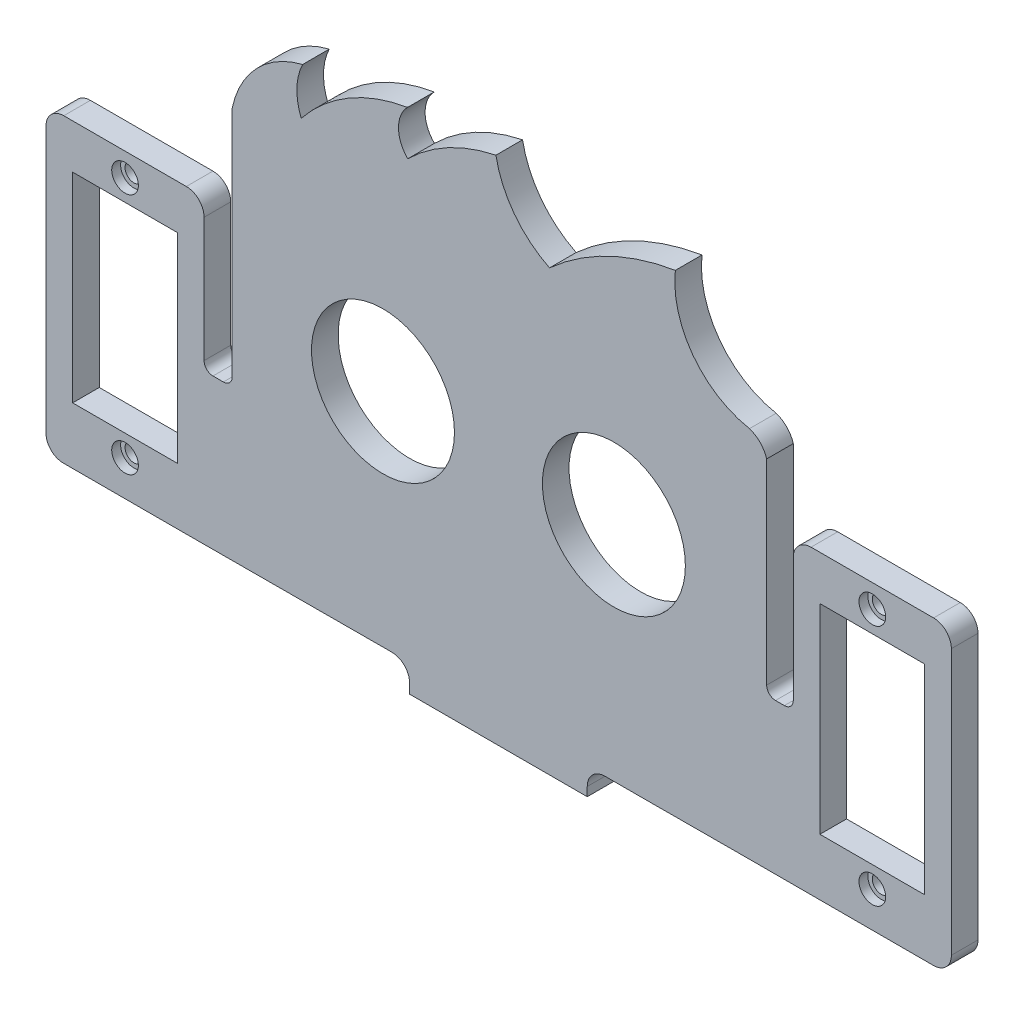
SolidWorks part; units mm, degrees
ref_plane "Alzado" through (0, 0, 0) normal (0, 0, 1) x (1, 0, 0)
ref_plane "Planta" through (0, 0, 0) normal (0, 1, 0) x (1, 0, 0)
ref_plane "Vista lateral" through (0, 0, 0) normal (1, 0, 0) x (0, 0, -1)
sketch "Model" plane through (0, 0, 0) normal (0, 0, 1) x (1, 0, 0)
  line L0 (28.5553, -36.0989) -> (29.723, -36.0989)
  line L4 (27.5553, -21.121) -> (27.5553, -35.0989)
  line L7 (70.699, -56.058) -> (50.699, -56.058)
  line L8 (92.899, -36.071) -> (91.899, -36.071)
  line L11 (90.899, -13.021) -> (90.899, -35.071)
  line L14 (96.899, -46.621) -> (108.699, -46.621)
  line L15 (108.699, -46.621) -> (108.699, -24.121)
  line L16 (108.699, -24.121) -> (96.899, -24.121)
  line L17 (96.899, -24.121) -> (96.899, -46.621)
  line L18 (12.7553, -24.121) -> (12.7553, -46.621)
  line L19 (12.7553, -46.621) -> (24.5553, -46.621)
  line L20 (24.5553, -46.621) -> (24.5553, -24.121)
  line L21 (24.5553, -24.121) -> (12.7553, -24.121)
  line L22 (93.899, -35.071) -> (93.899, -21.121)
  line L26 (72.699, -53.058) -> (76.899, -53.058)
  line L27 (73.699, -28.021) -> (47.699, -28.021) construction
  line L28 (60.699, -28.021) -> (60.699, -66.5104) construction
  line L29 (60.699, -56.058) -> (60.699, -18.5514) construction
  line L30 (70.699, -56.058) -> (70.699, -55.058)
  line L31 (50.699, -56.058) -> (50.699, -54.9616)
  line L32 (25.6116, -53.0206) -> (48.6939, -52.9617)
  line L53 (30.723, -8.8986) -> (30.723, -35.0989)
  line L55 (88.899, -53.021) -> (76.899, -53.058)
  line L61 (109.699, -19.121) -> (95.899, -19.121)
  line L62 (111.699, -51.021) -> (111.699, -21.121)
  line L63 (109.699, -53.021) -> (88.899, -53.021)
  line L95 (9.7553, -21.121) -> (9.7553, -51.0769)
  line L96 (25.5553, -19.121) -> (11.7553, -19.121)
  line L98 (25.6116, -53.0206) -> (11.699, -53.0206)
  circle A8 centre (73.699, -28.021) radius 8.05
  circle A9 centre (47.699, -28.021) radius 8.05
  circle A10 centre (102.799, -21.721) radius 1
  circle A11 centre (102.799, -49.021) radius 1
  circle A12 centre (18.6553, -49.021) radius 1
  circle A13 centre (18.6553, -21.721) radius 1
  arc A14 (91.899, -36.071) -> (90.899, -35.071) centre (91.899, -35.071) cw
  arc A15 (92.899, -36.071) -> (93.899, -35.071) centre (92.899, -35.071) ccw
  arc A16 (29.723, -36.0989) -> (30.723, -35.0989) centre (29.723, -35.0989) ccw
  arc A17 (28.5553, -36.0989) -> (27.5553, -35.0989) centre (28.5553, -35.0989) cw
  arc A18 (50.699, -54.9616) -> (48.6939, -52.9617) centre (48.699, -54.9616) ccw
  arc A19 (70.699, -55.058) -> (72.699, -53.058) centre (72.699, -55.058) cw
  arc A35 (38.6464, -0.6811) -> (30.723, -8.8986) centre (41.1528, -11.0265) ccw
  arc A36 (38.6464, -0.6811) -> (38.4994, -6.0039) centre (44.5214, -3.5068) ccw
  arc A37 (50.467, 1.0514) -> (38.4994, -6.0039) centre (53.655, -18.0341) ccw
  arc A38 (50.467, 1.0514) -> (50.49, -3.9486) centre (52.9785, -1.4371) ccw
  arc A39 (60.4156, 1.3614) -> (50.49, -3.9486) centre (64.4081, -18.0332) ccw
  arc A40 (60.4156, 1.3614) -> (66.4524, -6.6109) centre (71.4063, 3.4121) ccw
  arc A41 (80.6205, 0.2365) -> (66.4524, -6.6109) centre (85.1982, -27.3168) ccw
  arc A42 (80.6205, 0.2365) -> (88.9687, -11.0265) centre (90.866, -0.8949) ccw
  arc A43 (90.899, -13.021) -> (88.9687, -11.0265) centre (88.0226, -13.8735) ccw
  arc A46 (95.899, -19.121) -> (93.899, -21.121) centre (95.899, -21.121) ccw
  arc A47 (111.699, -21.121) -> (109.699, -19.121) centre (109.699, -21.121) ccw
  arc A48 (109.699, -53.021) -> (111.699, -51.021) centre (109.699, -51.021) ccw
  arc A63 (9.7553, -51.0769) -> (11.699, -53.0206) centre (11.699, -51.0769) ccw
  arc A64 (11.7553, -19.121) -> (9.7553, -21.121) centre (11.7553, -21.121) ccw
  arc A65 (27.5553, -21.121) -> (25.5553, -19.121) centre (25.5553, -21.121) ccw
  point P37 (70.699, -53.058)
  dimension "D1" = 1
  dimension "D4" = 2
  dimension "D2" = 20
  dimension "D3" = 3
extrude "Saliente-Extruir1" add sketch "Model" along normal blind 3
sketch "Croquis1" plane through (0, 0, 0) normal (0, 0, -1) x (-1, 0, 0)
  line L0 (-70.699, -56.058) -> (-70.699, -53.058)
  line L1 (-70.699, -53.058) -> (-50.699, -53.058)
  line L2 (-50.699, -53.058) -> (-50.699, -56.058)
  line L21 (-48.6939, -52.9617) -> (-25.6116, -53.0206)
  line L22 (-25.6116, -53.0206) -> (-11.699, -53.0206)
  line L23 (-9.7553, -51.0769) -> (-9.7553, -21.121)
  line L24 (-11.7553, -19.121) -> (-25.5553, -19.121)
  line L25 (-27.5553, -21.121) -> (-27.5553, -35.0989)
  line L26 (-28.5553, -36.0989) -> (-29.723, -36.0989)
  line L27 (-30.723, -35.0989) -> (-30.723, -8.8986)
  line L28 (-90.899, -13.021) -> (-90.899, -35.071)
  line L29 (-91.899, -36.071) -> (-92.899, -36.071)
  line L30 (-93.899, -35.071) -> (-93.899, -21.121)
  line L31 (-95.899, -19.121) -> (-109.699, -19.121)
  line L32 (-111.699, -21.121) -> (-111.699, -51.021)
  line L33 (-109.699, -53.021) -> (-88.899, -53.021)
  line L34 (-88.899, -53.021) -> (-76.899, -53.058)
  line L35 (-76.899, -53.058) -> (-72.699, -53.058)
  line L36 (-70.699, -55.058) -> (-70.699, -56.058)
  line L37 (-70.699, -56.058) -> (-50.699, -56.058)
  line L38 (-50.699, -56.058) -> (-50.699, -54.9616)
  line L55 (-70.699, -56.058) -> (-50.699, -56.058)
  arc A21 (-48.6939, -52.9617) -> (-50.699, -54.9616) centre (-48.699, -54.9616) ccw
  arc A22 (-11.699, -53.0206) -> (-9.7553, -51.0769) centre (-11.699, -51.0769) ccw
  arc A23 (-9.7553, -21.121) -> (-11.7553, -19.121) centre (-11.7553, -21.121) ccw
  arc A24 (-25.5553, -19.121) -> (-27.5553, -21.121) centre (-25.5553, -21.121) ccw
  arc A25 (-28.5553, -36.0989) -> (-27.5553, -35.0989) centre (-28.5553, -35.0989) ccw
  arc A26 (-30.723, -35.0989) -> (-29.723, -36.0989) centre (-29.723, -35.0989) ccw
  arc A27 (-30.723, -8.8986) -> (-38.6464, -0.6811) centre (-41.1528, -11.0265) ccw
  arc A28 (-38.4994, -6.0039) -> (-38.6464, -0.6811) centre (-44.5214, -3.5068) ccw
  arc A29 (-38.4994, -6.0039) -> (-50.467, 1.0514) centre (-53.655, -18.0341) ccw
  arc A30 (-50.49, -3.9486) -> (-50.467, 1.0514) centre (-52.9785, -1.4371) ccw
  arc A31 (-50.49, -3.9486) -> (-60.4156, 1.3614) centre (-64.4081, -18.0332) ccw
  arc A32 (-66.4524, -6.6109) -> (-60.4156, 1.3614) centre (-71.4063, 3.4121) ccw
  arc A33 (-66.4524, -6.6109) -> (-80.6205, 0.2365) centre (-85.1982, -27.3168) ccw
  arc A34 (-88.9687, -11.0265) -> (-80.6205, 0.2365) centre (-90.866, -0.8949) ccw
  arc A35 (-88.9687, -11.0265) -> (-90.899, -13.021) centre (-88.0226, -13.8735) ccw
  arc A36 (-91.899, -36.071) -> (-90.899, -35.071) centre (-91.899, -35.071) ccw
  arc A37 (-93.899, -35.071) -> (-92.899, -36.071) centre (-92.899, -35.071) ccw
  arc A38 (-93.899, -21.121) -> (-95.899, -19.121) centre (-95.899, -21.121) ccw
  arc A39 (-109.699, -19.121) -> (-111.699, -21.121) centre (-109.699, -21.121) ccw
  arc A40 (-111.699, -51.021) -> (-109.699, -53.021) centre (-109.699, -51.021) ccw
  arc A41 (-70.699, -55.058) -> (-72.699, -53.058) centre (-72.699, -55.058) ccw
  dimension "D1" = 3
  dimension "D2" = 0
extrude "Saliente-Extruir2" add sketch "Croquis1" along normal blind 8
sketch "Croquis2" plane through (0, -53.058, 0) normal (0, 1, 0) x (1, 0, 0)
  line L0 (60.699, 8) -> (60.699, 0) construction
  line L1 (50.699, 8) -> (70.699, 8) construction
  line L2 (50.699, 0) -> (70.699, 0) construction
  circle A0 centre (66.699, 3.5) radius 1.5
  circle A1 centre (54.699, 3.5) radius 1.5
  dimension "D1" = 6
  dimension "D2" = 3.5
extrude "Cortar-Extruir1" cut sketch "Croquis2" against normal blind 3
fillet "Redondeo2" radius 2 2 edges at (50.699, -54.558, -8) (70.699, -54.558, -8)
sketch "Croquis3" plane through (0, 0, 3) normal (0, 0, 1) x (1, 0, 0)
  circle A0 centre (18.6553, -21.721) radius 1.5
  circle A1 centre (18.6553, -49.021) radius 1.5
  circle A2 centre (102.799, -49.021) radius 1.5
  circle A3 centre (102.799, -21.721) radius 1.5
extrude "Cortar-Extruir2" cut sketch "Croquis3" against normal blind 1
sketch "Croquis4" plane through (0, -53.058, 0) normal (0, 1, 0) x (1, 0, 0)
  circle A0 centre (54.699, 3.5) radius 2.25
  circle A1 centre (66.699, 3.5) radius 2.25
extrude "Cortar-Extruir3" cut sketch "Croquis4" against normal blind 1
